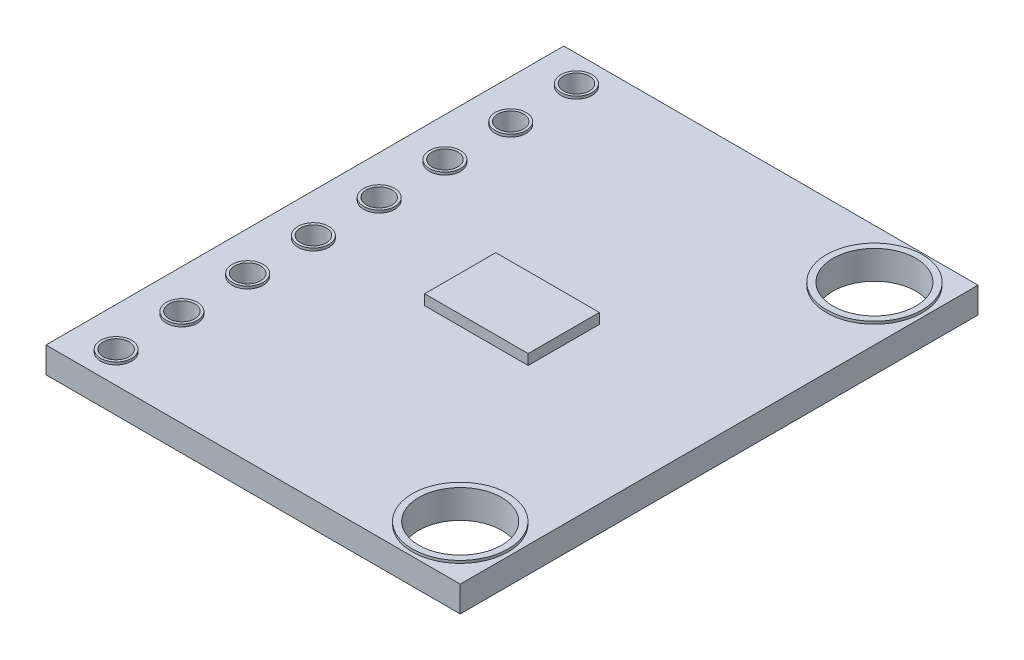
SolidWorks part; units mm, degrees
ref_plane "Front Plane" through (0, 0, 0) normal (0, 0, 1) x (1, 0, 0)
ref_plane "Top Plane" through (0, 0, 0) normal (0, 1, 0) x (1, 0, 0)
ref_plane "Right Plane" through (0, 0, 0) normal (1, 0, 0) x (0, 0, -1)
sketch "Sketch1" plane through (0, 0, 0) normal (0, 1, 0) x (1, 0, 0)
  line L1 (-8, -10) -> (8, -10)
  line L2 (-8, -10) -> (-8, 10)
  line L3 (-8, 10) -> (8, 10)
  line L4 (8, -10) -> (8, 10)
  line L5 (-8, -10) -> (8, 10) construction
  line L6 (-8, 10) -> (8, -10) construction
  point P0 (0, 0)
  dimension "D1" = 16
  dimension "D2" = 20
extrude "Boss-Extrude1" add sketch "Sketch1" along normal blind 1
sketch "Sketch4" plane through (0, 1, 0) normal (0, 1, 0) x (1, 0, 0)
  line L1 (-2, -1.375) -> (2, -1.375)
  line L2 (-2, -1.375) -> (-2, 1.375)
  line L3 (-2, 1.375) -> (2, 1.375)
  line L4 (2, -1.375) -> (2, 1.375)
  line L5 (-2, -1.375) -> (2, 1.375) construction
  line L6 (-2, 1.375) -> (2, -1.375) construction
  point P0 (0, 0)
  dimension "D1" = 2.75
  dimension "D2" = 4
extrude "Boss-Extrude3" add sketch "Sketch4" along normal blind 0.4 separate body
sketch "Çizim1" plane through (0, 1, 0) normal (0, 1, 0) x (1, 0, 0)
  line L1 (-8, -10) -> (8, -10) construction
  circle A0 centre (-6.4008, -8.89) radius 0.5
  circle A1 centre (-6.4008, -6.35) radius 0.5
  circle A2 centre (-6.4008, -3.81) radius 0.5
  circle A3 centre (-6.4008, -1.27) radius 0.5
  circle A4 centre (-6.4008, 1.27) radius 0.5
  circle A5 centre (-6.4008, 3.81) radius 0.5
  circle A6 centre (-6.4008, 6.35) radius 0.5
  circle A7 centre (-6.4008, 8.89) radius 0.5
  circle A8 centre (-6.4008, -8.89) radius 0.6
  circle A9 centre (-6.4008, -6.35) radius 0.6
  circle A10 centre (-6.4008, -3.81) radius 0.6
  circle A11 centre (-6.4008, -1.27) radius 0.6
  circle A12 centre (-6.4008, 1.27) radius 0.6
  circle A13 centre (-6.4008, 3.81) radius 0.6
  circle A14 centre (-6.4008, 6.35) radius 0.6
  circle A15 centre (-6.4008, 8.89) radius 0.6
  dimension "D1" = 1
  dimension "D2" = 1
  dimension "D3" = 2.54
  dimension "D4" = 1
  dimension "D5" = 1
  dimension "D6" = 1
  dimension "D7" = 1
  dimension "D8" = 1
  dimension "D9" = 1
  dimension "D10" = 2.54
  dimension "D11" = 2.54
  dimension "D12" = 2.54
  dimension "D13" = 2.54
  dimension "D14" = 2.54
  dimension "D15" = 2.54
  dimension "D16" = 1.11
  dimension "D17" = 17.78
  dimension "D18" = 0.1
  dimension "D19" = 0.1
  dimension "D20" = 0.1
  dimension "D21" = 0.1
  dimension "D22" = 0.1
  dimension "D23" = 0.1
  dimension "D24" = 0.1
  dimension "D25" = 0.1
extrude "Yükseklik-Ekstrüzyon1" add sketch "Çizim1" along normal blind 0.1
sketch "Çizim3" plane through (0, 1, 0) normal (0, 1, 0) x (1, 0, 0)
  circle A0 centre (-6.4008, -8.89) radius 0.5
  circle A1 centre (-6.4008, -6.35) radius 0.5
  circle A2 centre (-6.4008, -3.81) radius 0.5
  circle A3 centre (-6.4008, -1.27) radius 0.5
  circle A4 centre (-6.4008, 1.27) radius 0.5
  circle A5 centre (-6.4008, 3.81) radius 0.5
  circle A6 centre (-6.4008, 6.35) radius 0.5
  circle A7 centre (-6.4008, 8.89) radius 0.5
  dimension "D1" = 1
  dimension "D2" = 1
  dimension "D3" = 1
  dimension "D4" = 1
  dimension "D5" = 1
  dimension "D6" = 1
  dimension "D7" = 1
  dimension "D8" = 1
extrude "Kes-Ekstrüzyon2" cut sketch "Çizim3" against normal blind 20.1
sketch "Çizim4" plane through (0, 1, 0) normal (0, 1, 0) x (1, 0, 0)
  line L0 (8, 10) -> (-8, 10) construction
  line L1 (8, -10) -> (8, 10) construction
  line L2 (-8, -10) -> (8, -10) construction
  circle A0 centre (6, -8) radius 1.6
  circle A1 centre (6, 8) radius 1.6
  circle A2 centre (6, -8) radius 1.85
  circle A3 centre (6, 8) radius 1.85
  dimension "D1" = 3.2
  dimension "D2" = 3.2
  dimension "D3" = 2
  dimension "D4" = 2
  dimension "D5" = 2
  dimension "D6" = 2
  dimension "D7" = 0.25
  dimension "D8" = 0.25
extrude "Yükseklik-Ekstrüzyon2" add sketch "Çizim4" along normal blind 0.1
sketch "Çizim5" plane through (0, 1, 0) normal (0, 1, 0) x (1, 0, 0)
  circle A0 centre (6, 8) radius 1.6
  circle A1 centre (6, -8) radius 1.6
  dimension "D1" = 3.2
  dimension "D2" = 3.2
extrude "Kes-Ekstrüzyon3" cut sketch "Çizim5" against normal blind 10.1
